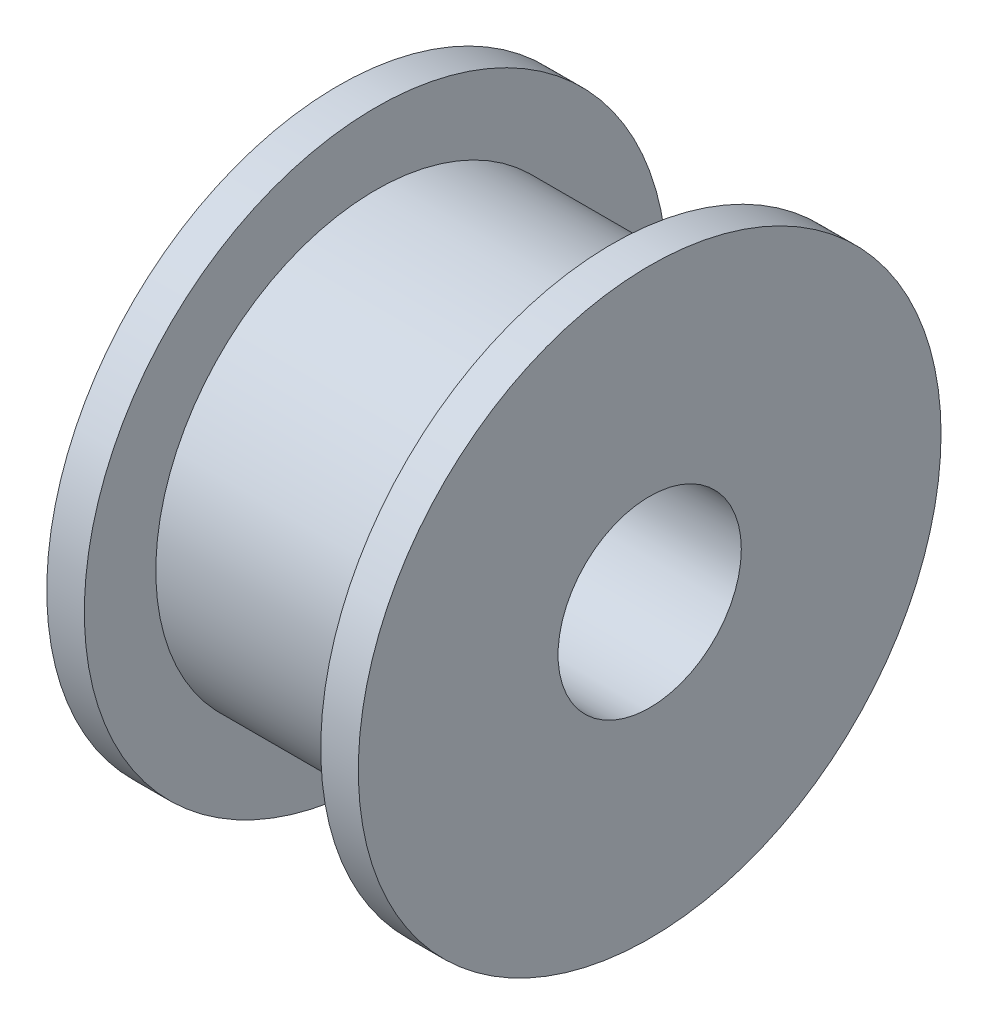
SolidWorks part; units mm, degrees
material "6061-T6 (SS)"
ref_plane "Front Plane" through (0, 0, 0) normal (0, 0, 1) x (1, 0, 0)
ref_plane "Top Plane" through (0, 0, 0) normal (0, 1, 0) x (1, 0, 0)
ref_plane "Right Plane" through (0, 0, 0) normal (1, 0, 0) x (0, 0, -1)
sketch "Sketch1" plane through (0, 0, 0) normal (0, 0, 1) x (1, 0, 0)
  line L0 (8.2688, 7.95) -> (8.2688, 2.5)
  line L1 (8.2688, 7.95) -> (9.2938, 7.95)
  line L2 (9.2938, 7.95) -> (9.2938, 6)
  line L3 (9.2938, 6) -> (15.7438, 6)
  line L4 (15.7438, 6) -> (15.7438, 7.95)
  line L5 (15.7438, 7.95) -> (16.7688, 7.95)
  line L6 (16.7688, 7.95) -> (16.7688, 2.5)
  line L7 (16.7688, 2.5) -> (8.2688, 2.5)
  line L8 (0, 0) -> (-7.6744, 0) construction
  dimension "D1" = 5
  dimension "D2" = 15.9
  dimension "D3" = 12
  dimension "D4" = 6.45
  dimension "D5" = 8.5
revolve "Revolve1" add sketch "Sketch1" angle 360 about L8
ref_plane "Plano1" through (12.5188, 0, 0) normal (1, 0, 0) x (0, 0, -1)
sketch "Croquis1" plane through (12.5188, 0, 0) normal (1, 0, 0) x (0, 0, -1)
  line L1 (-9.5496, 9.359) -> (10.6129, 9.359)
  line L2 (-9.5496, 9.359) -> (-9.5496, -10.1013)
  line L3 (-9.5496, -10.1013) -> (10.6129, -10.1013)
  line L4 (10.6129, 9.359) -> (10.6129, -10.1013)
move or copy body "Sólido-Mover/Copiar1" [suppressed] bodies to move or copy 101
